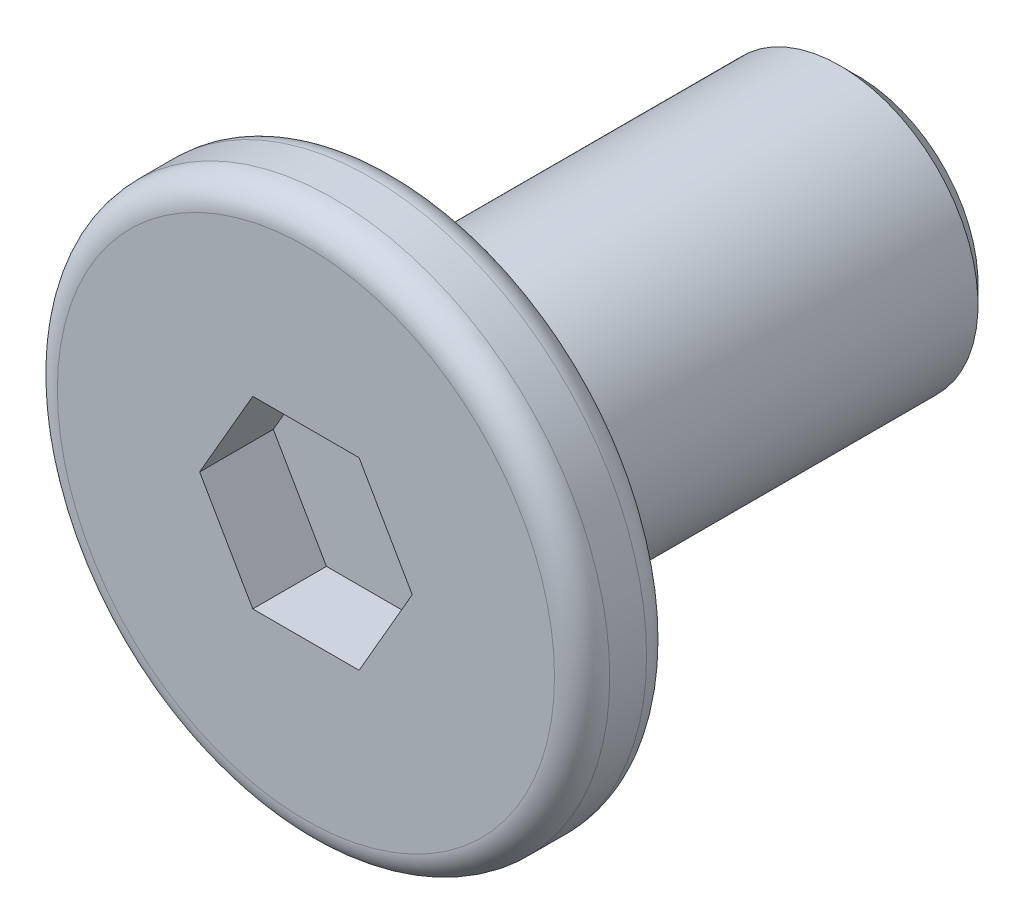
SolidWorks part; units mm, degrees
ref_plane "前视基准面" through (0, 0, 0) normal (0, 0, 1) x (1, 0, 0)
ref_plane "上视基准面" through (0, 0, 0) normal (0, 1, 0) x (1, 0, 0)
ref_plane "右视基准面" through (0, 0, 0) normal (1, 0, 0) x (0, 0, -1)
sketch "草图1" plane through (0, 0, 0) normal (0, 0, 1) x (1, 0, 0)
  circle A0 centre (0, 0) radius 3
  dimension "D1" = 6
extrude "凸台-拉伸1" add sketch "草图1" along normal mid plane 1
sketch "草图2" plane through (0, 0, -0.5) normal (0, 0, -1) x (-1, 0, 0)
  circle A0 centre (0, 0) radius 1.5
  dimension "D1" = 3
extrude "凸台-拉伸2" add sketch "草图2" along normal blind 5
chamfer "倒角1" distance 0.2 angle 45 1 edges at (-1.5, 0, -5.5)
sketch "草图3" plane through (0, 0, 0.5) normal (0, 0, 1) x (1, 0, 0)
  line L1 (1.1547, 0) -> (0.5774, 1)
  line L2 (0.5774, 1) -> (-0.5774, 1)
  line L3 (-0.5774, 1) -> (-1.1547, 0)
  line L4 (-1.1547, 0) -> (-0.5774, -1)
  line L5 (-0.5774, -1) -> (0.5774, -1)
  line L6 (0.5774, -1) -> (1.1547, 0)
  circle A0 centre (0, 0) radius 1 construction
  dimension "D1" = 2
extrude "切除-拉伸1" cut sketch "草图3" against normal blind 0.8
fillet "圆角2" radius 0.3 2 edges at (3, 0, -0.5) (3, 0, 0.5)
